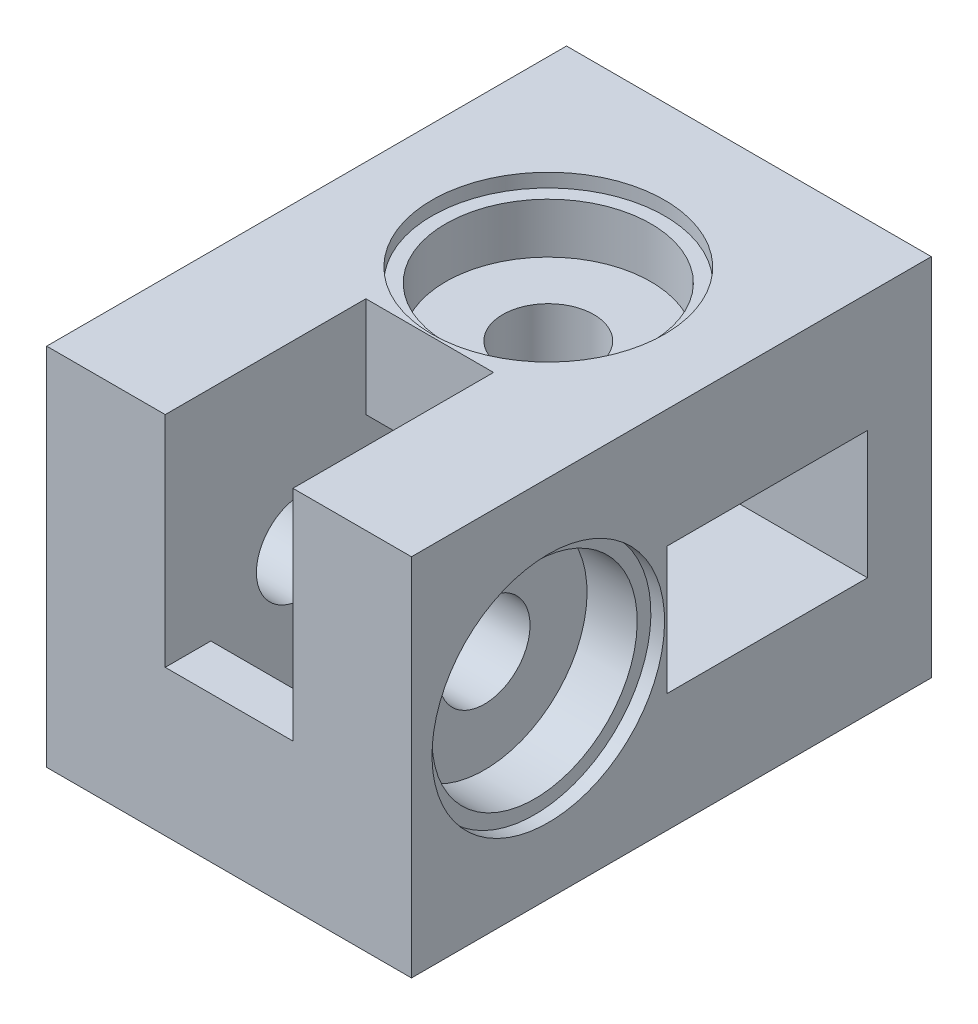
SolidWorks part; units mm, degrees
ref_plane "Plan de face" through (0, 0, 0) normal (0, 0, 1) x (1, 0, 0)
ref_plane "Plan de dessus" through (0, 0, 0) normal (0, 1, 0) x (1, 0, 0)
ref_plane "Plan de droite" through (0, 0, 0) normal (1, 0, 0) x (0, 0, -1)
sketch "Esquisse1" plane through (0, 0, 0) normal (0, 0, 1) x (1, 0, 0)
  line L1 (-40, 40) -> (0, 40)
  line L2 (-40, 40) -> (-40, 0)
  line L3 (-40, 0) -> (0, 0)
  line L4 (0, 40) -> (0, 0)
  dimension "D1" = 40
  dimension "D2" = 40
extrude "Boss.-Extru.1" add sketch "Esquisse1" along normal blind 50
sketch "Esquisse2" plane through (0, 40, 0) normal (0, 1, 0) x (1, 0, 0)
  line L0 (0, 0) -> (-40, 0) construction
  line L1 (-40, -50) -> (-40, 0) construction
  circle A0 centre (-20, -15) radius 5
  dimension "D1" = 10
  dimension "D2" = 15
  dimension "D3" = 20
extrude "Enlèv. mat.-Extru.1" cut sketch "Esquisse2" against normal through all
sketch "Esquisse3" plane through (-40, 0, 0) normal (-1, 0, 0) x (0, 0, 1)
  line L0 (50, 40) -> (50, 0) construction
  line L1 (50, 40) -> (0, 40) construction
  circle A0 centre (35, 20) radius 5
  dimension "D1" = 10
  dimension "D2" = 15
  dimension "D3" = 20
extrude "Enlèv. mat.-Extru.2" cut sketch "Esquisse3" against normal through all
sketch "Esquisse4" plane through (-40, 0, 0) normal (-1, 0, 0) x (0, 0, 1)
  line L1 (25, 27) -> (5, 27)
  line L2 (25, 27) -> (25, 13)
  line L3 (25, 13) -> (5, 13)
  line L4 (5, 27) -> (5, 13)
  line L5 (0, 40) -> (0, 0) construction
  line L6 (50, 0) -> (0, 0) construction
  line L7 (50, 40) -> (0, 40) construction
  dimension "D1" = 14
  dimension "D2" = 20
  dimension "D3" = 5
  dimension "D4" = 13
  dimension "D5" = 13
extrude "Enlèv. mat.-Extru.3" cut sketch "Esquisse4" against normal blind 29
sketch "Esquisse5" plane through (0, 0, 0) normal (0, -1, 0) x (1, 0, 0)
  line L0 (-40, 50) -> (0, 50) construction
  line L1 (-13, 25) -> (-27, 25)
  line L2 (-13, 25) -> (-13, 45)
  line L3 (-13, 45) -> (-27, 45)
  line L4 (-27, 25) -> (-27, 45)
  line L5 (-40, 50) -> (-40, 0) construction
  dimension "D1" = 20
  dimension "D2" = 5
  dimension "D3" = 14
  dimension "D4" = 13
extrude "Enlèv. mat.-Extru.4" cut sketch "Esquisse5" against normal blind 29
sketch "Esquisse6" plane through (0, 0, 0) normal (1, 0, 0) x (0, 0, -1)
  line L0 (0, 0) -> (0, 40) construction
  line L1 (0, 27) -> (-22, 27)
  line L2 (0, 27) -> (0, 13)
  line L3 (0, 13) -> (-22, 13)
  line L4 (-22, 27) -> (-22, 13)
  line L5 (-50, 0) -> (0, 0) construction
  dimension "D1" = 14
  dimension "D2" = 22
  dimension "D3" = 13
extrude "Enlèv. mat.-Extru.5" cut sketch "Esquisse6" against normal blind 24
sketch "Esquisse7" plane through (0, 40, 0) normal (0, 1, 0) x (1, 0, 0)
  line L0 (0, -50) -> (-40, -50) construction
  line L1 (-27, -50) -> (-13, -50)
  line L2 (-27, -50) -> (-27, -28)
  line L3 (-27, -28) -> (-13, -28)
  line L4 (-13, -50) -> (-13, -28)
  line L5 (-40, -50) -> (-40, 0) construction
  dimension "D1" = 14
  dimension "D2" = 22
  dimension "D3" = 13
extrude "Enlèv. mat.-Extru.6" cut sketch "Esquisse7" against normal blind 24
sketch "Esquisse8" plane through (0, 0, 0) normal (1, 0, 0) x (0, 0, -1)
  circle A0 centre (-35, 20) radius 11.25
  dimension "D1" = 22.5
extrude "Enlèv. mat.-Extru.7" cut sketch "Esquisse8" against normal blind 7
sketch "Esquisse9" plane through (0, 0, 0) normal (1, 0, 0) x (0, 0, -1)
  circle A0 centre (-35, 20) radius 12.75
  dimension "D1" = 25.5
extrude "Enlèv. mat.-Extru.8" cut sketch "Esquisse9" against normal blind 1.5
sketch "Esquisse10" plane through (0, 40, 0) normal (0, 1, 0) x (1, 0, 0)
  circle A0 centre (-20, -15) radius 11.25
  dimension "D1" = 22.5
extrude "Enlèv. mat.-Extru.9" cut sketch "Esquisse10" against normal blind 7
sketch "Esquisse11" plane through (0, 40, 0) normal (0, 1, 0) x (1, 0, 0)
  circle A0 centre (-20, -15) radius 12.75
  dimension "D1" = 25.5
extrude "Enlèv. mat.-Extru.10" cut sketch "Esquisse11" against normal blind 1.5
sketch "Esquisse12" plane through (0, 0, 0) normal (0, 0, -1) x (-1, 0, 0)
  line L1 (40, 40) -> (0, 40)
  line L2 (40, 40) -> (40, 0)
  line L3 (40, 0) -> (0, 0)
  line L4 (0, 40) -> (0, 0)
extrude "Boss.-Extru.2" add sketch "Esquisse12" along normal blind 7
sketch "Esquisse13" plane through (0, 0, -7) normal (0, 0, -1) x (-1, 0, 0)
  line L0 (40, 40) -> (0, 40) construction
  line L1 (0, 40) -> (0, 0) construction
  circle A0 centre (10, 7.5) radius 2.25
  circle A1 centre (32.5, 30) radius 2.25
  dimension "D1" = 4.5
  dimension "D2" = 4.5
  dimension "D3" = 32.5
  dimension "D4" = 32.5
  dimension "D5" = 10
  dimension "D6" = 10
extrude "Enlèv. mat.-Extru.11" cut sketch "Esquisse13" against normal blind 15
sketch "Esquisse14" plane through (-40, 0, 0) normal (-1, 0, 0) x (0, 0, 1)
  line L0 (50, 40) -> (-7, 40) construction
  line L1 (0.5, 33.75) -> (-3, 33.75)
  line L2 (0.5, 33.75) -> (0.5, 26.25)
  line L3 (0.5, 26.25) -> (-3, 26.25)
  line L4 (-3, 33.75) -> (-3, 26.25)
  line L5 (-7, 0) -> (-7, 40) construction
  dimension "D1" = 3.5
  dimension "D2" = 7.5
  dimension "D3" = 6.25
  dimension "D4" = 4
extrude "Enlèv. mat.-Extru.12" cut sketch "Esquisse14" against normal blind 12
sketch "Esquisse15" plane through (0, 0, 0) normal (0, -1, 0) x (1, 0, 0)
  line L0 (0, -7) -> (-40, -7) construction
  line L1 (-6.25, -3) -> (-13.75, -3)
  line L2 (-6.25, -3) -> (-6.25, 0.5)
  line L3 (-6.25, 0.5) -> (-13.75, 0.5)
  line L4 (-13.75, -3) -> (-13.75, 0.5)
  line L5 (0, 50) -> (0, -7) construction
  dimension "D1" = 7.5
  dimension "D2" = 3.5
  dimension "D3" = 4
  dimension "D4" = 6.25
extrude "Enlèv. mat.-Extru.13" cut sketch "Esquisse15" against normal blind 12
